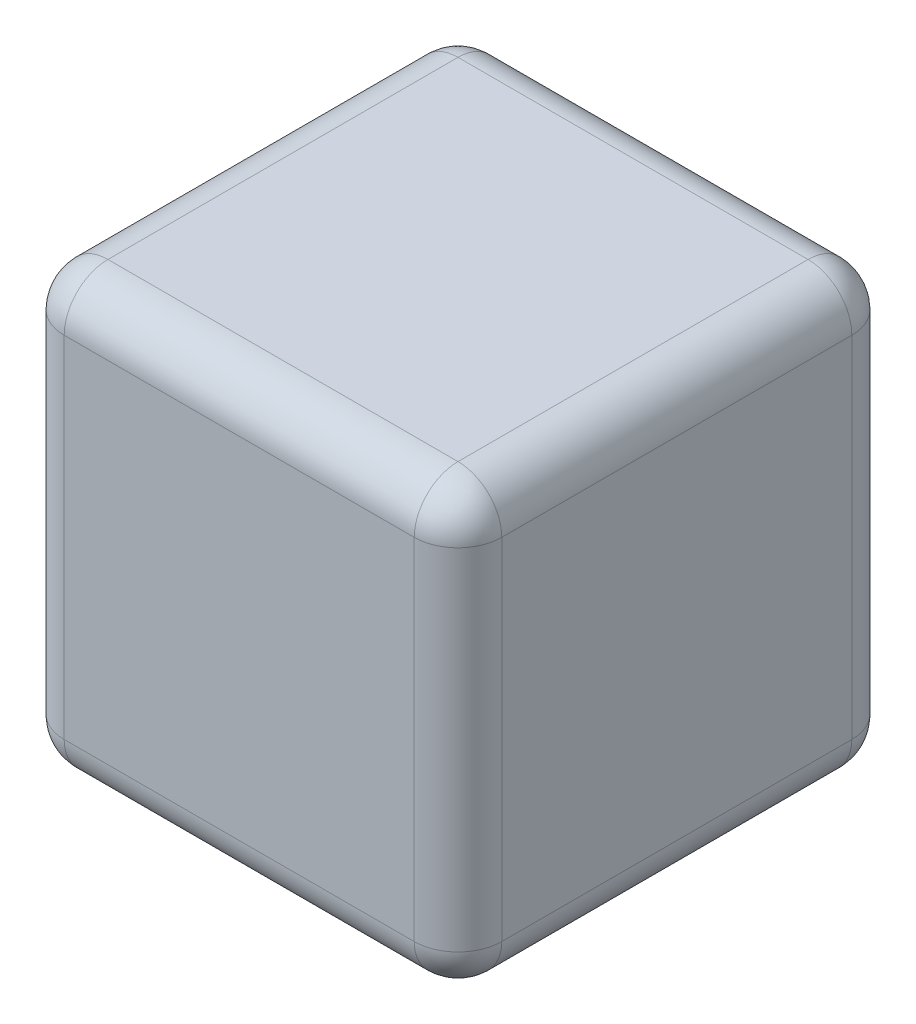
SolidWorks part; units mm, degrees
ref_plane "Front Plane" through (0, 0, 0) normal (0, 0, 1) x (1, 0, 0)
ref_plane "Top Plane" through (0, 0, 0) normal (0, 1, 0) x (1, 0, 0)
ref_plane "Right Plane" through (0, 0, 0) normal (1, 0, 0) x (0, 0, -1)
sketch "Sketch1" plane through (0, 0, 0) normal (0, 1, 0) x (1, 0, 0)
  line L0 (0, 0) -> (0, 25.4)
  line L1 (0, 25.4) -> (25.4, 25.4)
  line L2 (25.4, 25.4) -> (25.4, 0)
  line L3 (25.4, 0) -> (0, 0)
  dimension "D1" = 25.4
extrude "Boss-Extrude1" add sketch "Sketch1" along normal blind 25.4
fillet "Fillet1" radius 2.54 12 edges at (0, 0, -12.7) (0, 12.7, -25.4) (12.7, 0, -25.4) (0, 12.7, 0) (12.7, 0, 0) (25.4, 12.7, 0) (25.4, 12.7, -25.4) (25.4, 0, -12.7) (0, 25.4, -12.7) (12.7, 25.4, -25.4) (25.4, 25.4, -12.7) (12.7, 25.4, 0)
